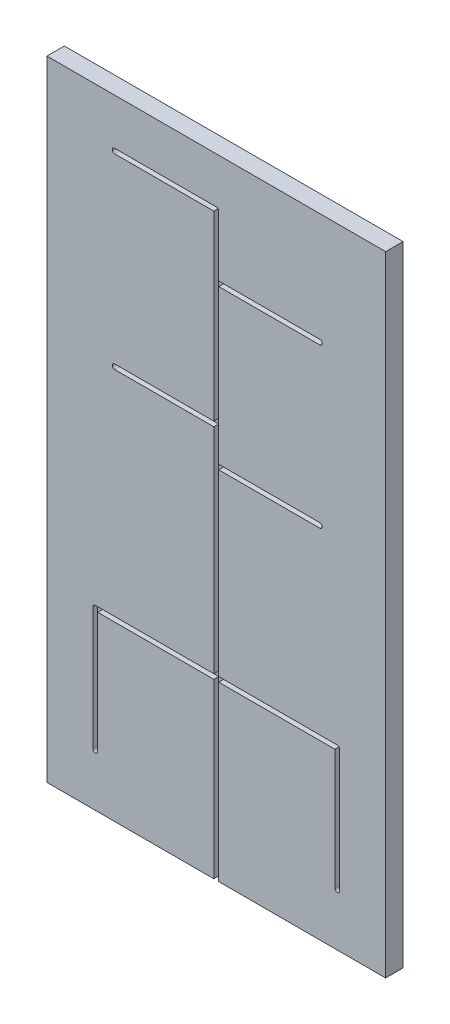
SolidWorks part; units mm, degrees
material "Balza"
ref_plane "Přední rovina" through (0, 0, 0) normal (0, 0, 1) x (1, 0, 0)
ref_plane "Horní rovina" through (0, 0, 0) normal (0, 1, 0) x (1, 0, 0)
ref_plane "Pravá rovina" through (0, 0, 0) normal (1, 0, 0) x (0, 0, -1)
sketch "Skica1" plane through (0, 0, 0) normal (0, 0, 1) x (1, 0, 0)
  line L1 (0, 0) -> (350, 0)
  line L2 (0, 0) -> (0, 650)
  line L3 (0, 650) -> (350, 650)
  line L4 (350, 0) -> (350, 650)
  dimension "D1" = 650
  dimension "D2" = 350
extrude "Přidat vysunutím2" add sketch "Skica1" along normal blind 18
sketch "vetsi" plane through (0, 0, 18) normal (0, 0, 1) x (1, 0, 0)
  line L0 (175, -1000) -> (175, 49000) construction
  line L1 (175, 600) -> (175, 0) construction
  line L2 (-829.0853, 0) -> (49170.9147, 0) construction
  line L14 (190, 600) -> (190, 0)
  line L15 (160, 600) -> (160, 0)
  line L16 (300, 181) -> (50, 181) construction
  line L17 (300, 166) -> (50, 166)
  line L18 (300, 196) -> (50, 196)
  line L19 (50, 181) -> (50, 54) construction
  line L20 (65, 181) -> (65, 54)
  line L21 (35, 181) -> (35, 54)
  line L22 (300, 181) -> (300, 54) construction
  line L25 (315, 181) -> (315, 54)
  line L26 (285, 181) -> (285, 54)
  line L28 (175, 371) -> (282, 371) construction
  line L29 (175, 386) -> (282, 386)
  line L30 (175, 356) -> (282, 356)
  line L31 (175, 407) -> (70, 407) construction
  line L32 (175, 392) -> (70, 392)
  line L33 (175, 422) -> (70, 422)
  line L34 (175, 535) -> (282, 535) construction
  line L35 (175, 550) -> (282, 550)
  line L36 (175, 520) -> (282, 520)
  line L37 (175, 600) -> (70, 600) construction
  line L38 (175, 585) -> (70, 585)
  line L39 (175, 615) -> (70, 615)
  arc A2 (190, 600) -> (160, 600) centre (175, 600) ccw
  arc A3 (160, 0) -> (190, 0) centre (175, 0) ccw
  arc A4 (300, 166) -> (300, 196) centre (300, 181) ccw
  arc A5 (50, 196) -> (50, 166) centre (50, 181) ccw
  arc A6 (65, 181) -> (35, 181) centre (50, 181) ccw
  arc A7 (35, 54) -> (65, 54) centre (50, 54) ccw
  arc A10 (315, 181) -> (285, 181) centre (300, 181) ccw
  arc A11 (285, 54) -> (315, 54) centre (300, 54) ccw
  arc A12 (175, 386) -> (175, 356) centre (175, 371) ccw
  arc A13 (282, 356) -> (282, 386) centre (282, 371) ccw
  arc A14 (175, 392) -> (175, 422) centre (175, 407) ccw
  arc A15 (70, 422) -> (70, 392) centre (70, 407) ccw
  arc A16 (175, 550) -> (175, 520) centre (175, 535) ccw
  arc A17 (282, 520) -> (282, 550) centre (282, 535) ccw
  arc A18 (175, 585) -> (175, 615) centre (175, 600) ccw
  arc A19 (70, 615) -> (70, 585) centre (70, 600) ccw
  point P5 (175, 300)
  point P13 (175, 181)
  point P20 (50, 117.5)
  point P27 (300, 117.5)
  point P34 (228.5, 371)
  point P42 (122.5, 407)
  point P49 (228.5, 535)
  point P56 (122.5, 600)
  line M9 (0, 0) -> (350, 0)
  dimension "D6" = 15
  dimension "D1" = 15
  dimension "D3" = 15
  dimension "D7" = 15
  dimension "D11" = 15
  dimension "D12" = 15
  dimension "D14" = 15
  dimension "D16" = 15
  dimension "D17" = 15
  dimension "D2" = 181
  dimension "D4" = 250
  dimension "D5" = 181
  dimension "D8" = 127
  dimension "D9" = 127
  dimension "D10" = 175
  dimension "D13" = 107
  dimension "D15" = 105
  dimension "D18" = 107
  dimension "D19" = 105
  dimension "D20" = 371
  dimension "D21" = 407
  dimension "D22" = 535
  dimension "D23" = 600
sketch "mensi" plane through (0, 0, 18) normal (0, 0, 1) x (1, 0, 0)
  line L0 (175, -1019.8645) -> (175, 48980.1355) construction
  line L1 (175, 600) -> (175, 0) construction
  line L2 (-901.1125, 0) -> (49098.8875, 0) construction
  line L3 (177.5, 600) -> (177.5, 0)
  line L4 (172.5, 600) -> (172.5, 0)
  line L5 (300, 181) -> (50, 181) construction
  line L6 (300, 178.5) -> (50, 178.5)
  line L7 (300, 183.5) -> (50, 183.5)
  line L8 (50, 181) -> (50, 54) construction
  line L9 (52.5, 181) -> (52.5, 54)
  line L10 (47.5, 181) -> (47.5, 54)
  line L11 (300, 181) -> (300, 54) construction
  line L12 (302.5, 181) -> (302.5, 54)
  line L13 (297.5, 181) -> (297.5, 54)
  line L14 (175, 371) -> (282, 371) construction
  line L15 (175, 373.5) -> (282, 373.5)
  line L16 (175, 368.5) -> (282, 368.5)
  line L17 (175, 407) -> (70, 407) construction
  line L18 (175, 404.5) -> (70, 404.5)
  line L19 (175, 409.5) -> (70, 409.5)
  line L20 (175, 535) -> (282, 535) construction
  line L21 (175, 537.5) -> (282, 537.5)
  line L22 (175, 532.5) -> (282, 532.5)
  line L23 (175, 600) -> (70, 600) construction
  line L24 (175, 597.5) -> (70, 597.5)
  line L25 (175, 602.5) -> (70, 602.5)
  arc A0 (177.5, 600) -> (172.5, 600) centre (175, 600) ccw
  arc A1 (172.5, 0) -> (177.5, 0) centre (175, 0) ccw
  arc A2 (300, 178.5) -> (300, 183.5) centre (300, 181) ccw
  arc A3 (50, 183.5) -> (50, 178.5) centre (50, 181) ccw
  arc A4 (52.5, 181) -> (47.5, 181) centre (50, 181) ccw
  arc A5 (47.5, 54) -> (52.5, 54) centre (50, 54) ccw
  arc A6 (302.5, 181) -> (297.5, 181) centre (300, 181) ccw
  arc A7 (297.5, 54) -> (302.5, 54) centre (300, 54) ccw
  arc A8 (175, 373.5) -> (175, 368.5) centre (175, 371) ccw
  arc A9 (282, 368.5) -> (282, 373.5) centre (282, 371) ccw
  arc A10 (175, 404.5) -> (175, 409.5) centre (175, 407) ccw
  arc A11 (70, 409.5) -> (70, 404.5) centre (70, 407) ccw
  arc A12 (175, 537.5) -> (175, 532.5) centre (175, 535) ccw
  arc A13 (282, 532.5) -> (282, 537.5) centre (282, 535) ccw
  arc A14 (175, 597.5) -> (175, 602.5) centre (175, 600) ccw
  arc A15 (70, 602.5) -> (70, 597.5) centre (70, 600) ccw
  point P5 (175, 300)
  point P13 (175, 181)
  point P20 (50, 117.5)
  point P27 (300, 117.5)
  point P34 (228.5, 371)
  point P41 (122.5, 407)
  point P48 (228.5, 535)
  point P55 (122.5, 600)
  point P60 (175, 0)
  line M1 (0, 650) -> (0, 0)
  line M2 (0, 0) -> (350, 0)
  line M3 (350, 0) -> (350, 650)
  line M4 (350, 650) -> (0, 650)
  dimension "D1" = 2.5
  dimension "D2" = 2.5
  dimension "D4" = 2.5
  dimension "D5" = 2.5
  dimension "D8" = 2.5
  dimension "D9" = 2.5
  dimension "D11" = 2.5
  dimension "D13" = 2.5
  dimension "D14" = 2.5
  dimension "D3" = 250
  dimension "D6" = 127
  dimension "D7" = 127
  dimension "D10" = 107
  dimension "D12" = 105
  dimension "D15" = 107
  dimension "D16" = 105
  dimension "D17" = 371
  dimension "D18" = 407
  dimension "D19" = 535
  dimension "D20" = 600
  dimension "D21" = 181
extrude "Odebrat vysunutím1" cut sketch "vetsi" against normal blind 15 contours L21 A7 L20 L17 A5 | L20 A6 A5 L17 | A6 L20 L17 L15 L18 | L14 L17 L15 M9 | L14 L18 L15 L17 | A10 L18 L14 L17 L26 | A4 A10 L26 L17 | L26 A11 L25 A4 L17 | A12 L15 L18 L14 L30 | L30 A13 L29 L14 | L29 A12 L30 L14 | A14 L32 L15 A12 L29 L14 | A14 L33 L15 L32 | L33 A15 L32 L15 | A16 L15 L33 A14 L14 L36 | L35 A16 L36 L14 | L36 A17 L35 L14 | A18 L38 L15 A16 L35 L14 | L38 A18 A2 L15 | L39 A19 L38 L15 A2
extrude "Přidat vysunutím3" add sketch "mensi" against normal blind 5 contours A15 L25 A0 L3 L21 A13 L22 L15 A9 L16 L7 A2 L12 A7 L13 L6 L4 L9 A5 L10 A3 L18 A11 L19 L24 M2 M3 M4 M1
